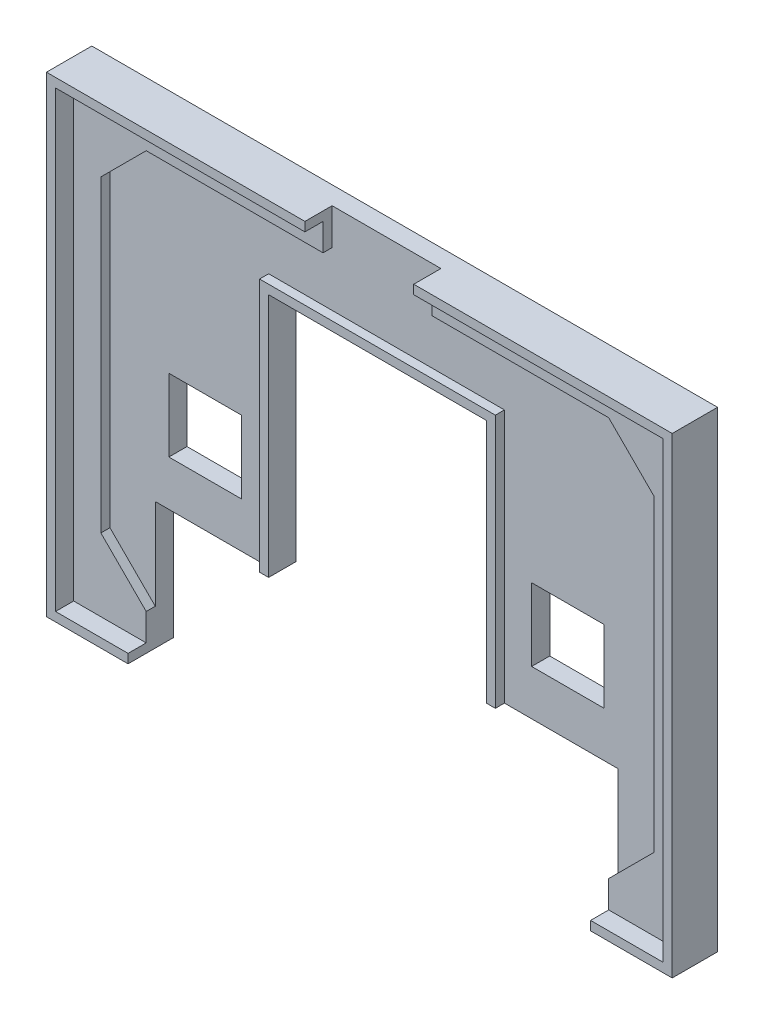
SolidWorks part; units mm, degrees
ref_plane "Přední rovina" through (0, 0, 0) normal (0, 0, 1) x (1, 0, 0)
ref_plane "Horní rovina" through (0, 0, 0) normal (0, 1, 0) x (1, 0, 0)
ref_plane "Pravá rovina" through (0, 0, 0) normal (1, 0, 0) x (0, 0, -1)
sketch "Skica1" plane through (0, 0, 0) normal (0, 0, 1) x (1, 0, 0)
  line L1 (-33.5, -25) -> (33.5, -25)
  line L2 (-33.5, -25) -> (-33.5, 25)
  line L3 (-33.5, 25) -> (33.5, 25)
  line L4 (33.5, -25) -> (33.5, 25)
  line L5 (-33.5, -25) -> (33.5, 25) construction
  line L6 (-33.5, 25) -> (33.5, -25) construction
  point P0 (0, 0)
  dimension "D1" = 67
  dimension "D2" = 50
extrude "Přidat vysunutím1" add sketch "Skica1" along normal blind 3
sketch "Skica2" plane through (0, 0, 3) normal (0, 0, 1) x (1, 0, 0)
  line L0 (-1000, 0) -> (49000, 0) construction
  line L1 (0, -1000) -> (0, 49000) construction
  line L2 (-1000, -22) -> (49000, -22) construction
  line L3 (-25.5, -1000) -> (-25.5, 49000) construction
  line L4 (-30.5, -1000) -> (-30.5, 49000) construction
  line L6 (-33.5, -25) -> (33.5, -25) construction
  line L7 (-25.5, -22) -> (-30.5, -17)
  line L8 (-30.5, -17) -> (-30.5, 17)
  line L9 (-25.5, -22) -> (25.5, -22)
  line L10 (30.5, -17) -> (30.5, 17)
  line L11 (25.5, -22) -> (30.5, -17)
  line L12 (25.5, 22) -> (30.5, 17)
  line L13 (-25.5, 22) -> (25.5, 22)
  line L14 (-25.5, 22) -> (-30.5, 17)
  point P20 (0, -22)
  point P21 (30.5, 0)
  point P24 (-30.5, 0)
  dimension "D1" = 30.5
  dimension "D2" = 5
  dimension "D3" = 3
  dimension "D4" = 45
extrude "Odebrat vysunutím1" cut sketch "Skica2" against normal offset from surface (1 mm away) 2 up to face at (0, 0, 0)
sketch "Skica3" plane through (0, 0, 0) normal (0, 0, -1) x (-1, 0, 0)
  line L0 (0, -1000) -> (0, 49000) construction
  line L1 (33.5, -25) -> (-33.5, -25) construction
  line L2 (24, 1) -> (16, 1)
  line L3 (24, 1) -> (24, -7)
  line L4 (24, -7) -> (16, -7)
  line L5 (16, 1) -> (16, -7)
  line L6 (-16, 1) -> (-16, -7)
  line L7 (33.5, -25) -> (-33.5, -25) construction
  line L8 (25.5, -25) -> (-25.5, -25)
  line L9 (25.5, -25) -> (25.5, -12)
  line L11 (-25.5, -25) -> (-25.5, -12)
  line L12 (-24, -7) -> (-16, -7)
  line L13 (25.5, -12) -> (12, -12)
  line L15 (12, -12) -> (12, 15)
  line L16 (12, 15) -> (-12, 15)
  line L17 (-12, -12) -> (-12, 15)
  line L18 (-12, -12) -> (-25.5, -12)
  line L19 (-24, 1) -> (-24, -7)
  line L20 (-24, 1) -> (-16, 1)
  dimension "D1" = 16
  dimension "D2" = 8
  dimension "D3" = 18
  dimension "D4" = 13
  dimension "D5" = 51
  dimension "D6" = 24
  dimension "D7" = 27
extrude "Odebrat vysunutím2" cut sketch "Skica3" against normal through all
sketch "Skica4" plane through (0, 0, 2) normal (0, 0, 1) x (1, 0, 0)
  line L0 (12, 15) -> (12, -12) construction
  line L1 (-12, -12) -> (-12, 15) construction
  line L2 (-12, 15) -> (12, 15) construction
  line L3 (12, 15) -> (12, -12)
  line L4 (-12, -12) -> (-12, 15)
  line L5 (-12, 15) -> (12, 15)
extrude "Vysunout tenkostěnný1" add sketch "Skica4" along normal up to surface (1 mm away) thin up to face at (0, -3.5714, 3) thin type one direction reverse wall 1
sketch "Skica5" plane through (0, 0, 0) normal (0, 0, -1) x (-1, 0, 0)
  line L0 (-33.5, 25) -> (33.5, 25) construction
  line L1 (33.5, 25) -> (33.5, -25) construction
  line L2 (33.5, -25) -> (25.5, -25) construction
  line L3 (-33.5, -25) -> (-33.5, 25) construction
  line L4 (-25.5, -25) -> (-33.5, -25) construction
  line L5 (-33.5, 25) -> (33.5, 25)
  line L6 (33.5, 25) -> (33.5, -25)
  line L7 (33.5, -25) -> (25.5, -25)
  line L8 (-33.5, -25) -> (-33.5, 25)
  line L9 (-25.5, -25) -> (-33.5, -25)
extrude "Vysunout tenkostěnný2" add sketch "Skica5" against normal blind 5 thin thin type one direction reverse wall 1
sketch "Skica6" plane through (0, 0, 2) normal (0, 0, 1) x (1, 0, 0)
  line L0 (0, -1000) -> (0, 49000) construction
  line L1 (25.5, 22) -> (-25.5, 22) construction
  line L2 (-6, 22) -> (6, 22)
  line L3 (-6, 22) -> (-6, 26)
  line L4 (-6, 26) -> (6, 26)
  line L5 (6, 22) -> (6, 26)
  line L6 (34.5, 26) -> (-34.5, 26) construction
  dimension "D1" = 12
extrude "Odebrat vysunutím3" cut sketch "Skica6" along normal through all
sketch "Skica8" plane through (0, 0, 0) normal (0, 0, -1) x (-1, 0, 0)
  line L0 (-32.966, 24.1012) -> (-28.0602, 24.1012)
  line L1 (-28.0602, 24.1012) -> (-28.0602, 20.1275)
  line L2 (-28.0602, 20.1275) -> (-32.966, 20.1275)
  line L3 (-32.966, 20.1275) -> (-32.966, 24.1012)
  line L5 (-26.4639, 17.6746) -> (-26.4639, 18.9256)
  line L6 (-26.4639, 18.9256) -> (-30.6584, 18.9256)
  line L12 (-30.6848, 11.2234) -> (-29.3602, 11.2234)
  line L13 (-29.3602, 11.2234) -> (-29.3602, 12.6707)
  line L18 (-26.4639, 17.6746) -> (-26.4639, 18.9256)
  line L19 (-30.6584, 17.6746) -> (-30.6584, 18.9256)
  line L20 (-25.0676, 13.5471) -> (-21.5576, 13.5471)
  line L21 (-23.3126, 13.5471) -> (-23.3126, 9.3732)
  line L22 (-21.1082, 9.3732) -> (-25.517, 9.3732)
  line L23 (-32.0584, 17.6746) -> (-30.6584, 17.6746)
  line L24 (-28.0602, 12.6707) -> (-28.0602, 14.0198)
  line L25 (-23.3126, 8.4858) -> (-23.3126, 27.2909) construction
  line L26 (-30.6848, 9.8989) -> (-30.6848, 11.2234)
  line L27 (-30.6848, 9.8989) -> (-32.0584, 9.8989)
  line L28 (-32.0584, 17.6746) -> (-32.0584, 9.8989)
  line L29 (-28.0602, 14.0198) -> (-25.0676, 14.0198)
  line L30 (-25.0676, 17.6746) -> (-26.4639, 17.6746)
  line L31 (-25.517, 9.3732) -> (-25.517, 9.8989)
  line L32 (-25.517, 9.8989) -> (-26.3186, 9.8989)
  line L33 (-25.2999, 10.9259) -> (-26.3186, 10.9259)
  line L34 (-26.3186, 10.9259) -> (-26.3186, 9.8989)
  line L35 (-25.2999, 10.9259) -> (-25.2999, 10.1843)
  line L36 (-25.2999, 10.1843) -> (-24.5538, 10.1843)
  line L37 (-24.5538, 10.1843) -> (-24.5538, 11.9471)
  line L38 (-24.5538, 11.9471) -> (-25.0676, 11.9471)
  line L39 (-25.0676, 11.9471) -> (-25.0676, 13.5471)
  line L40 (-25.0676, 14.0198) -> (-25.0676, 17.6746)
  line L41 (-29.3602, 12.6707) -> (-28.0602, 12.6707)
  line L44 (-17.265, 12.6707) -> (-18.565, 12.6707)
  line L45 (-21.5576, 14.0198) -> (-21.5576, 17.6746)
  line L46 (-21.5576, 11.9471) -> (-21.5576, 13.5471)
  line L47 (-22.0714, 11.9471) -> (-21.5576, 11.9471)
  line L48 (-22.0714, 10.1843) -> (-22.0714, 11.9471)
  line L49 (-21.3253, 10.1843) -> (-22.0714, 10.1843)
  line L50 (-21.3253, 10.9259) -> (-21.3253, 10.1843)
  line L51 (-20.3066, 10.9259) -> (-20.3066, 9.8989)
  line L52 (-21.3253, 10.9259) -> (-20.3066, 10.9259)
  line L53 (-21.1082, 9.8989) -> (-20.3066, 9.8989)
  line L54 (-21.1082, 9.3732) -> (-21.1082, 9.8989)
  line L55 (-21.5576, 17.6746) -> (-20.1612, 17.6746)
  line L56 (-18.565, 14.0198) -> (-21.5576, 14.0198)
  line L57 (-14.5668, 17.6746) -> (-14.5668, 9.8989)
  line L58 (-15.9404, 9.8989) -> (-14.5668, 9.8989)
  line L59 (-15.9404, 9.8989) -> (-15.9404, 11.2234)
  line L60 (-18.565, 12.6707) -> (-18.565, 14.0198)
  line L61 (-14.5668, 17.6746) -> (-15.9668, 17.6746)
  line L62 (-15.9668, 17.6746) -> (-15.9668, 18.9256)
  line L63 (-20.1612, 17.6746) -> (-20.1612, 18.9256)
  line L64 (-17.265, 11.2234) -> (-17.265, 12.6707)
  line L65 (-15.9404, 11.2234) -> (-17.265, 11.2234)
  line L66 (-20.1612, 18.9256) -> (-15.9668, 18.9256)
  line L67 (-20.1612, 17.6746) -> (-20.1612, 18.9256)
  line L68 (-18.565, 20.1275) -> (-13.6592, 20.1275)
  line L69 (-18.565, 24.1012) -> (-18.565, 20.1275)
  line L70 (-13.6592, 24.1012) -> (-18.565, 24.1012)
  line L71 (-13.6592, 20.1275) -> (-13.6592, 24.1012)
  line L72 (-34.5, -26) -> (-34.5, 26) construction
  line L73 (-25.5, -26) -> (-34.5, -26) construction
  line L74 (0, 0) -> (0, 33.1104) construction
  line L75 (23.3126, 8.4858) -> (23.3126, 27.2909) construction
  line L76 (13.6592, 20.1275) -> (13.6592, 24.1012)
  line L77 (13.6592, 24.1012) -> (18.565, 24.1012)
  line L78 (18.565, 24.1012) -> (18.565, 20.1275)
  line L79 (18.565, 20.1275) -> (13.6592, 20.1275)
  line L80 (20.1612, 17.6746) -> (20.1612, 18.9256)
  line L81 (20.1612, 18.9256) -> (15.9668, 18.9256)
  line L82 (15.9404, 11.2234) -> (17.265, 11.2234)
  line L83 (17.265, 11.2234) -> (17.265, 12.6707)
  line L84 (20.1612, 17.6746) -> (20.1612, 18.9256)
  line L85 (15.9668, 17.6746) -> (15.9668, 18.9256)
  line L86 (14.5668, 17.6746) -> (15.9668, 17.6746)
  line L87 (18.565, 12.6707) -> (18.565, 14.0198)
  line L88 (15.9404, 9.8989) -> (15.9404, 11.2234)
  line L89 (15.9404, 9.8989) -> (14.5668, 9.8989)
  line L90 (14.5668, 17.6746) -> (14.5668, 9.8989)
  line L91 (18.565, 14.0198) -> (21.5576, 14.0198)
  line L92 (21.5576, 17.6746) -> (20.1612, 17.6746)
  line L93 (21.1082, 9.3732) -> (21.1082, 9.8989)
  line L94 (21.1082, 9.8989) -> (20.3066, 9.8989)
  line L95 (21.3253, 10.9259) -> (20.3066, 10.9259)
  line L96 (20.3066, 10.9259) -> (20.3066, 9.8989)
  line L97 (21.3253, 10.9259) -> (21.3253, 10.1843)
  line L98 (21.3253, 10.1843) -> (22.0714, 10.1843)
  line L99 (22.0714, 10.1843) -> (22.0714, 11.9471)
  line L100 (22.0714, 11.9471) -> (21.5576, 11.9471)
  line L101 (21.5576, 11.9471) -> (21.5576, 13.5471)
  line L102 (21.5576, 14.0198) -> (21.5576, 17.6746)
  line L103 (17.265, 12.6707) -> (18.565, 12.6707)
  line L104 (29.3602, 12.6707) -> (28.0602, 12.6707)
  line L105 (25.0676, 14.0198) -> (25.0676, 17.6746)
  line L106 (25.0676, 11.9471) -> (25.0676, 13.5471)
  line L107 (24.5538, 11.9471) -> (25.0676, 11.9471)
  line L108 (24.5538, 10.1843) -> (24.5538, 11.9471)
  line L109 (25.2999, 10.1843) -> (24.5538, 10.1843)
  line L110 (25.2999, 10.9259) -> (25.2999, 10.1843)
  line L111 (26.3186, 10.9259) -> (26.3186, 9.8989)
  line L112 (25.2999, 10.9259) -> (26.3186, 10.9259)
  line L113 (25.517, 9.8989) -> (26.3186, 9.8989)
  line L114 (25.517, 9.3732) -> (25.517, 9.8989)
  line L115 (25.0676, 17.6746) -> (26.4639, 17.6746)
  line L116 (28.0602, 14.0198) -> (25.0676, 14.0198)
  line L117 (32.0584, 17.6746) -> (32.0584, 9.8989)
  line L118 (30.6848, 9.8989) -> (32.0584, 9.8989)
  line L119 (30.6848, 9.8989) -> (30.6848, 11.2234)
  line L120 (28.0602, 12.6707) -> (28.0602, 14.0198)
  line L121 (32.0584, 17.6746) -> (30.6584, 17.6746)
  line L122 (21.1082, 9.3732) -> (25.517, 9.3732)
  line L123 (23.3126, 13.5471) -> (23.3126, 9.3732)
  line L124 (25.0676, 13.5471) -> (21.5576, 13.5471)
  line L125 (30.6584, 17.6746) -> (30.6584, 18.9256)
  line L126 (26.4639, 17.6746) -> (26.4639, 18.9256)
  line L127 (29.3602, 11.2234) -> (29.3602, 12.6707)
  line L128 (30.6848, 11.2234) -> (29.3602, 11.2234)
  line L129 (26.4639, 18.9256) -> (30.6584, 18.9256)
  line L130 (26.4639, 17.6746) -> (26.4639, 18.9256)
  line L131 (32.966, 20.1275) -> (32.966, 24.1012)
  line L132 (28.0602, 20.1275) -> (32.966, 20.1275)
  line L133 (28.0602, 24.1012) -> (28.0602, 20.1275)
  line L134 (32.966, 24.1012) -> (28.0602, 24.1012)
  dimension "D1" = 1.534
  dimension "D2" = 2.4416
  dimension "D3" = 3.8152
  dimension "D4" = 3.8416
  dimension "D5" = 5.1398
  dimension "D6" = 6.4398
  dimension "D7" = 8.0361
  dimension "D8" = 8.1814
  dimension "D9" = 8.983
  dimension "D10" = 9.2001
  dimension "D11" = 9.4324
  dimension "D12" = 9.9462
  dimension "D13" = 11.1874
  dimension "D14" = 35.3732
  dimension "D15" = 35.8989
  dimension "D16" = 36.1843
  dimension "D17" = 36.9259
  dimension "D19" = 37.9471
  dimension "D20" = 38.6707
  dimension "D21" = 39.5471
  dimension "D22" = 40.0198
  dimension "D23" = 43.6746
  dimension "D24" = 44.9256
  dimension "D25" = 46.1275
  dimension "D26" = 50.1012
extrude "Odebrat vysunutím4" cut sketch "Skica8" against normal blind 1 contours L13 L41 L24 L29 L40 L30 L5 L6 L19 L23 L28 L27 L26 L12 | L3 L2 L1 L0 | L22 L54 L53 L51 L52 L50 L49 L48 L47 L46 L20 L21 | L39 L38 L37 L36 L35 L33 L34 L32 L31 L22 L21 L20 | L66 L63 L55 L45 L56 L60 L44 L64 L65 L59 L58 L57 L61 L62 | L68 L71 L70 L69 | L79 L78 L77 L76 | L83 L103 L87 L91 L102 L92 L80 L81 L85 L86 L90 L89 L88 L82 | L129 L126 L115 L105 L116 L120 L104 L127 L128 L119 L118 L117 L121 L125 | L131 L134 L133 L132 | L106 L124 L123 L122 L114 L113 L111 L112 L110 L109 L108 L107 | L123 L124 L101 L100 L99 L98 L97 L95 L96 L94 L93 L122
sketch "Skica9" plane through (0, 0, 1) normal (0, 0, -1) x (-1, 0, 0)
  line L0 (-28.0602, 14.0198) -> (-25.0676, 14.0198) construction
  line L1 (-29.3602, 15.3698) -> (-26.5639, 15.3698)
  line L2 (-29.3602, 15.3698) -> (-29.3602, 14.0198)
  line L3 (-29.3602, 14.0198) -> (-26.5639, 14.0198)
  line L4 (-26.5639, 15.3698) -> (-26.5639, 14.0198)
  line L5 (0, 0) -> (0, 32.3463) construction
  line L6 (17.265, 15.3698) -> (17.265, 14.0198)
  line L7 (-23.3126, 9.3732) -> (-23.3126, 17.1673) construction
  line L8 (-21.1082, 9.3732) -> (-25.517, 9.3732) construction
  line L9 (-17.265, 14.0198) -> (-20.0613, 14.0198)
  line L10 (-20.0613, 15.3698) -> (-20.0613, 14.0198)
  line L11 (-17.265, 15.3698) -> (-20.0613, 15.3698)
  line L12 (-17.265, 15.3698) -> (-17.265, 14.0198)
  line L13 (17.265, 15.3698) -> (20.0613, 15.3698)
  line L14 (20.0613, 15.3698) -> (20.0613, 14.0198)
  line L15 (17.265, 14.0198) -> (20.0613, 14.0198)
  line L16 (29.3602, 14.0198) -> (26.5639, 14.0198)
  line L17 (26.5639, 15.3698) -> (26.5639, 14.0198)
  line L18 (29.3602, 15.3698) -> (26.5639, 15.3698)
  line L19 (29.3602, 15.3698) -> (29.3602, 14.0198)
extrude "Přidat vysunutím2" add sketch "Skica9" along normal blind 1
sketch "Skica10" plane through (0, 0, 0) normal (0, 0, -1) x (-1, 0, 0)
  line L0 (34.5, 26) -> (34.5, -26) construction
  line L1 (34.5, -26) -> (25.5, -26) construction
  text T0 "PAND" font "BLOXAT" height 5.8
  dimension "D1" = 45.7089
  dimension "D2" = 43.2974
extrude "Odebrat vysunutím5" cut sketch "Skica10" against normal blind 1
